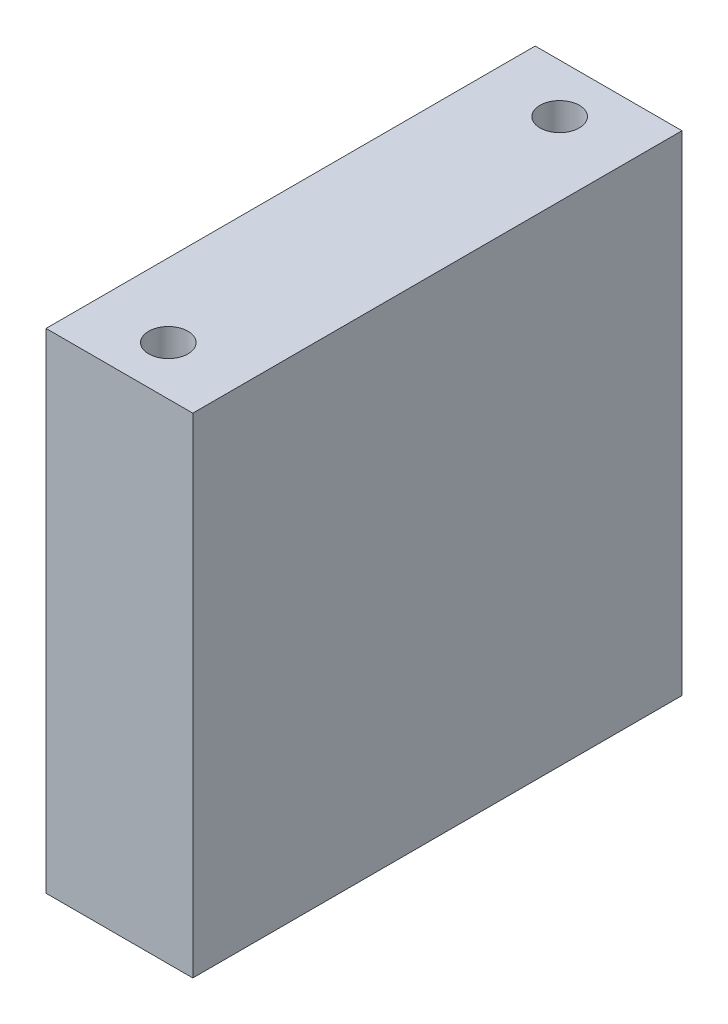
SolidWorks part; units mm, degrees
ref_plane "Front Plane" through (0, 0, 0) normal (0, 0, 1) x (1, 0, 0)
ref_plane "Top Plane" through (0, 0, 0) normal (0, 1, 0) x (1, 0, 0)
ref_plane "Right Plane" through (0, 0, 0) normal (1, 0, 0) x (0, 0, -1)
sketch "Sketch1" plane through (0, 0, 0) normal (0, 1, 0) x (1, 0, 0)
  line L1 (9.525, -31.75) -> (-9.525, -31.75)
  line L2 (9.525, -31.75) -> (9.525, 31.75)
  line L3 (9.525, 31.75) -> (-9.525, 31.75)
  line L4 (-9.525, -31.75) -> (-9.525, 31.75)
  line L5 (9.525, -31.75) -> (-9.525, 31.75) construction
  line L6 (9.525, 31.75) -> (-9.525, -31.75) construction
  point P0 (0, 0)
  dimension "D1" = 19.05
  dimension "D2" = 63.5
extrude "Boss-Extrude1" add sketch "Sketch1" along normal blind 63.5
hole_wizard "1/4-20 Tapped Hole1" positions "Sketch3" profile "Sketch4" tap size "1/4-20" standard "ANSI Inch"
sketch "Sketch3" plane through (0, 0, 0) normal (0, -1, 0) x (-1, 0, 0)
  line L0 (9.525, 31.75) -> (9.525, -31.75) construction
  line L1 (-9.525, 31.75) -> (9.525, 31.75) construction
  line L2 (9.525, -31.75) -> (-9.525, -31.75) construction
  point P0 (0, -25.4)
  point P2 (0, 25.4)
  dimension "D1" = 50.8
  dimension "D2" = 9.525
  dimension "D3" = 6.35
  dimension "D4" = 6.35
sketch "Sketch4" plane through (0, 0, 25.4) normal (1, 0, 0) x (0, 0, -1)
  line L0 (0, 0) -> (0, 18.0438)
  line L1 (0, 18.0438) -> (2.5527, 16.51)
  line L2 (2.5527, 16.51) -> (2.5527, 0)
  line L5 (2.5527, 0) -> (0, 0)
  line L10 (0, 18.0438) -> (-2.5527, 16.51) construction
  line L11 (0, -6.35) -> (0, 107.95) construction
  dimension "Tap Drill Dia." = 5.1054
  dimension "Tap Drill Depth" = 16.51
  dimension "Drill Angle" = 118
cosmetic thread "Hole Thread1" parameters "D1"=12.7, "D2"=6.35
cosmetic thread "Hole Thread2" parameters "D1"=12.7, "D2"=6.35
hole_wizard "1/4-20 Tapped Hole2" positions "Sketch5" profile "Sketch6" tap size "1/4-20" standard "ANSI Inch"
sketch "Sketch5" plane through (0, 63.5, 0) normal (0, 1, 0) x (1, 0, 0)
  line L0 (-9.525, -31.75) -> (9.525, -31.75) construction
  line L1 (9.525, 31.75) -> (-9.525, 31.75) construction
  line L2 (-9.525, 31.75) -> (-9.525, -31.75) construction
  point P0 (0, 25.4)
  point P2 (0, -25.4)
  point P9 (0, -18.0986)
  point P10 (0, 0)
  dimension "D1" = 50.8
  dimension "D2" = 6.35
  dimension "D3" = 6.35
  dimension "D4" = 9.525
sketch "Sketch6" plane through (0, 63.5, -25.4) normal (1, 0, 0) x (0, 0, 1)
  line L0 (0, 0) -> (0, 18.0438)
  line L1 (0, 18.0438) -> (2.5527, 16.51)
  line L2 (2.5527, 16.51) -> (2.5527, 0)
  line L5 (2.5527, 0) -> (0, 0)
  line L10 (0, 18.0438) -> (-2.5527, 16.51) construction
  line L11 (0, -6.35) -> (0, 107.95) construction
  dimension "Tap Drill Dia." = 5.1054
  dimension "Tap Drill Depth" = 16.51
  dimension "Drill Angle" = 118
cosmetic thread "Hole Thread3" parameters "D1"=12.7, "D2"=6.35
cosmetic thread "Hole Thread4" parameters "D1"=12.7, "D2"=6.35
